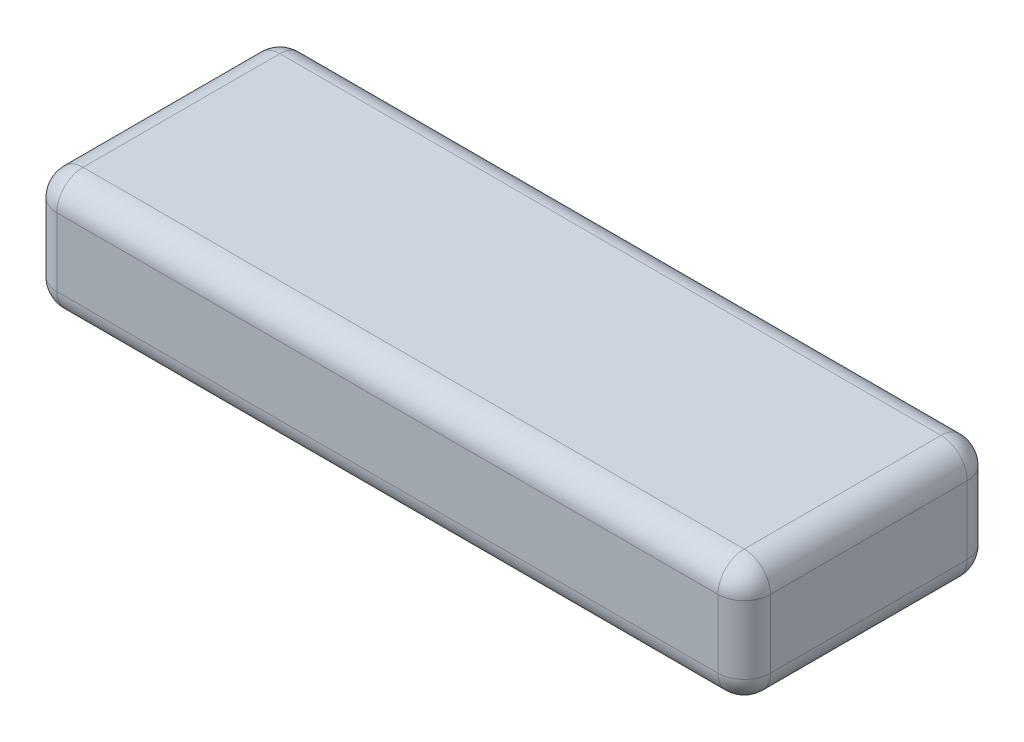
SolidWorks part; units mm, degrees
ref_plane "Front Plane" through (0, 0, 0) normal (0, 0, 1) x (1, 0, 0)
ref_plane "Top Plane" through (0, 0, 0) normal (0, 1, 0) x (1, 0, 0)
ref_plane "Right Plane" through (0, 0, 0) normal (1, 0, 0) x (0, 0, -1)
sketch "Sketch1" plane through (0, 0, 0) normal (0, 1, 0) x (1, 0, 0)
  line L1 (-68, 23.75) -> (68, 23.75)
  line L2 (-68, 23.75) -> (-68, -23.75)
  line L3 (-68, -23.75) -> (68, -23.75)
  line L4 (68, 23.75) -> (68, -23.75)
  point P4 (0, 23.75)
  point P6 (68, 0)
  dimension "D1" = 47.5
  dimension "D2" = 136
extrude "Boss-Extrude1" add sketch "Sketch1" along normal blind 23
fillet "Fillet1" radius 5 12 edges at (-68, 0, 0) (-68, 11.5, -23.75) (0, 0, -23.75) (-68, 11.5, 23.75) (0, 0, 23.75) (68, 0, 0) (68, 11.5, -23.75) (68, 11.5, 23.75) (68, 23, 0) (0, 23, 23.75) (0, 23, -23.75) (-68, 23, 0)
